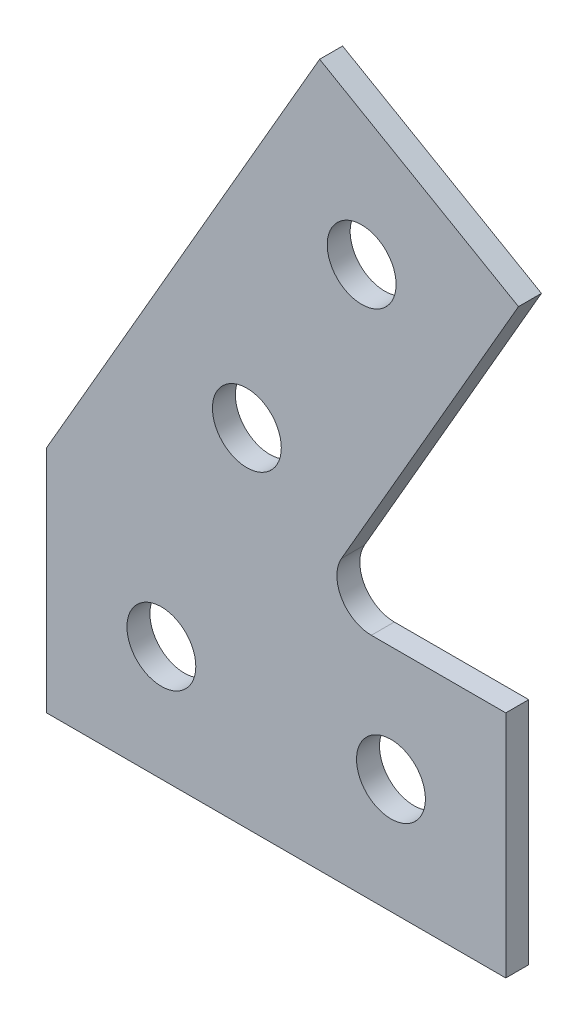
SolidWorks part; units mm, degrees
ref_plane "Front Plane" through (0, 0, 0) normal (0, 0, 1) x (1, 0, 0)
ref_plane "Top Plane" through (0, 0, 0) normal (0, 1, 0) x (1, 0, 0)
ref_plane "Right Plane" through (0, 0, 0) normal (1, 0, 0) x (0, 0, -1)
sketch "Esquisse1" plane through (0, 0, 0) normal (0, 0, 1) x (1, 0, 0)
  line L0 (0, 0) -> (20, 0)
  line L1 (20, 0) -> (20, 10)
  line L2 (20, 10) -> (14.1451, 10)
  line L3 (0, 0) -> (0, 10)
  line L4 (0, 10) -> (11.8934, 30.6)
  line L5 (12.846, 12.25) -> (20.5537, 25.6)
  line L6 (11.8934, 30.6) -> (20.5537, 25.6)
  circle A0 centre (5, 5) radius 1.5
  arc A1 (14.1451, 10) -> (12.846, 12.25) centre (14.1451, 11.5) cw
  circle A2 centre (15, 5) radius 1.5
  circle A3 centre (13.7235, 23.7699) radius 1.5
  circle A4 centre (8.7235, 15.1096) radius 1.5
  point P9 (20, 5)
  dimension "D7" = 1.5
  dimension "D8" = 3
  dimension "D9" = 10
  dimension "D1" = 10
  dimension "D2" = 20
  dimension "D3" = 150
  dimension "D4" = 10
  dimension "D5" = 30.6
  dimension "D6" = 5
  dimension "D10" = 5
  dimension "D11" = 5
  dimension "D12" = 10
  dimension "D13" = 5
extrude "Boss.-Extru.1" add sketch "Esquisse1" along normal blind 1
